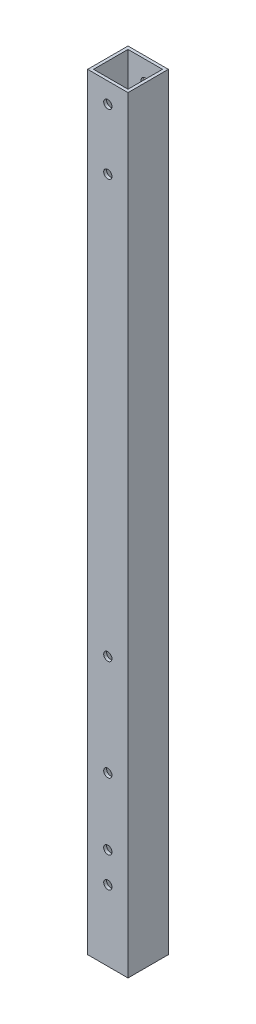
SolidWorks part; units mm, degrees
material "Thornel VCB-20 Carbon Cloth"
ref_plane "Front Plane" through (0, 0, 0) normal (0, 0, 1) x (1, 0, 0)
ref_plane "Top Plane" through (0, 0, 0) normal (0, 1, 0) x (1, 0, 0)
ref_plane "Right Plane" through (0, 0, 0) normal (1, 0, 0) x (0, 0, -1)
sketch "Sketch1" plane through (0, 0, 0) normal (0, 1, 0) x (1, 0, 0)
  line L0 (1.45, 18.55) -> (18.55, 18.55)
  line L1 (0, 0) -> (20, 0)
  line L2 (0, 0) -> (0, 20)
  line L3 (0, 20) -> (20, 20)
  line L4 (20, 0) -> (20, 20)
  line L5 (18.55, 1.45) -> (18.55, 18.55)
  line L6 (1.45, 1.45) -> (18.55, 1.45)
  line L7 (1.45, 1.45) -> (1.45, 18.55)
  dimension "D1" = 20
  dimension "D2" = 1.45
extrude "Boss-Extrude1" add sketch "Sketch1" along normal blind 350
sketch "Sketch2" plane through (0, 0, -20) normal (0, 0, -1) x (-1, 0, 0)
  line L0 (-20, 350) -> (0, 350) construction
  line L1 (-20, 350) -> (-20, 0) construction
  line L2 (-20, 0) -> (0, 0) construction
  circle A0 centre (-10, 340) radius 2.05
  circle A1 centre (-10, 310) radius 2.05
  circle A2 centre (-10, 20) radius 2.05
  circle A3 centre (-10, 5) radius 2.05
  dimension "D1" = 30
  dimension "D2" = 4.1
  dimension "D3" = 10
  dimension "D4" = 10
  dimension "D5" = 15
  dimension "D6" = 5
extrude "Cut-Extrude1" cut sketch "Sketch2" against normal through all
sketch "Sketch3" plane through (0, 0, -20) normal (0, 0, -1) x (-1, 0, 0)
  line L0 (-20, 0) -> (0, 0) construction
  line L1 (-20, 350) -> (0, 350) construction
  circle A0 centre (-10, 103) radius 2.05
  circle A1 centre (-10, 53) radius 2.05
  circle A2 centre (-10, 5) radius 2.05 construction
  point P7 (-10, 0)
  dimension "D1" = 50
  dimension "D2" = 247
extrude "Cut-Extrude2" cut sketch "Sketch3" against normal through all
sketch "Sketch4" plane through (0, 0, 0) normal (0, -1, 0) x (1, 0, 0)
  line L1 (0, 0) -> (20, 0)
  line L2 (0, 0) -> (0, -20)
  line L3 (0, -20) -> (20, -20)
  line L4 (20, 0) -> (20, -20)
  line L5 (18.55, -18.55) -> (1.45, -18.55)
  line L6 (18.55, -18.55) -> (18.55, -1.45)
  line L7 (18.55, -1.45) -> (1.45, -1.45)
  line L8 (1.45, -18.55) -> (1.45, -1.45)
extrude "Boss-Extrude2" add sketch "Sketch4" along normal blind 30
